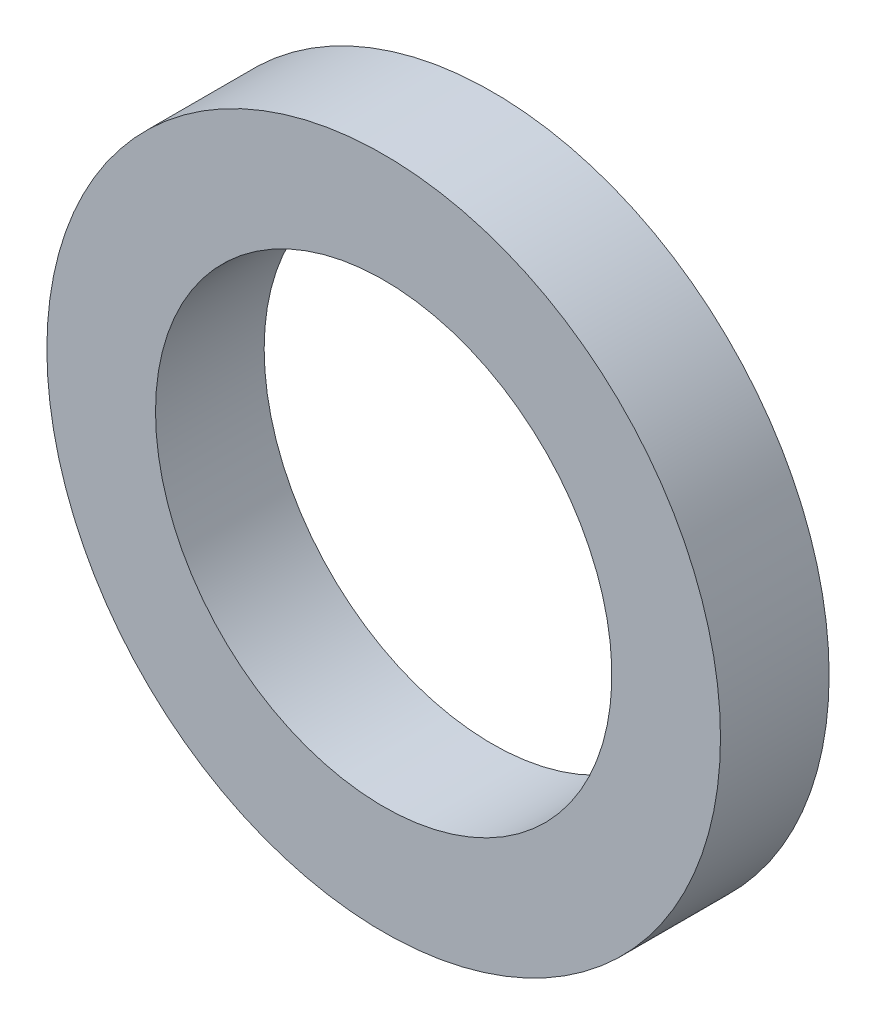
SolidWorks part; units mm, degrees
ref_plane "Front Plane" through (0, 0, 0) normal (0, 0, 1) x (1, 0, 0)
ref_plane "Top Plane" through (0, 0, 0) normal (0, 1, 0) x (1, 0, 0)
ref_plane "Right Plane" through (0, 0, 0) normal (1, 0, 0) x (0, 0, -1)
sketch "Sketch1" plane through (0, 0, 0) normal (0, 0, 1) x (1, 0, 0)
  line L0 (0, 0) -> (3.1, 0) construction
  line L1 (0, 0) -> (0, 3.1) construction
  circle A0 centre (0, 0) radius 1.5
  circle A1 centre (0, 0) radius 3.1
extrude "Boss-Extrude3" add sketch "Sketch1" along normal blind 1 contours A1
sketch "Sketch3" plane through (0, 0, 0) normal (0, 0, -1) x (-1, 0, 0)
  circle A0 centre (0, 0) radius 2.1
extrude "Cut-Extrude1" cut sketch "Sketch3" against normal through all
equation "\"ID\"= 3mm"
equation "\"OD\"= 6.2mm"
equation "\"D1@Sketch1\"= \"OD\" "
equation "\"D2@Sketch1\"= \"ID\""
equation "\"D1@Sketch3\"      = \"ID\" + 1.2mm"
equation "\"height\"= 9mm"
equation "\"D1@Boss-Extrude3\" = \"height\" - 8"
